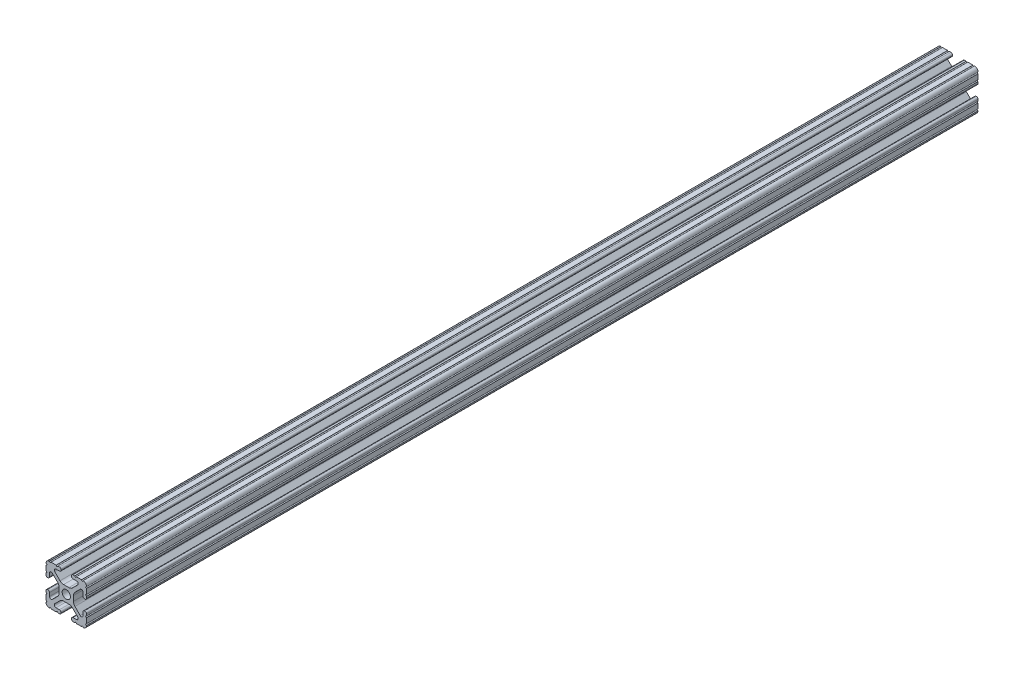
SolidWorks part; units mm, degrees
ref_plane "Front Plane" through (0, 0, 0) normal (0, 0, 1) x (1, 0, 0)
ref_plane "Top Plane" through (0, 0, 0) normal (0, 1, 0) x (1, 0, 0)
ref_plane "Right Plane" through (0, 0, 0) normal (1, 0, 0) x (0, 0, -1)
sketch "Sketch1" plane through (0, 0, 0) normal (0, 0, 1) x (1, 0, 0)
  line L88 (-7.1797, -8.6452) -> (-3.9523, -5.4237)
  line L89 (-1.7093, -4.4958) -> (1.7093, -4.4958)
  line L90 (3.9523, -5.4237) -> (7.1797, -8.6452)
  line L91 (6.4164, -10.4902) -> (4.2875, -10.4902)
  line L92 (3.2385, -11.5392) -> (3.2385, -11.651)
  line L93 (4.2875, -12.7) -> (5.3171, -12.7)
  line L94 (6.3331, -12.7) -> (9.5504, -12.7)
  line L95 (12.7, -9.5504) -> (12.7, -6.3331)
  line L96 (12.7, -5.3171) -> (12.7, -4.2875)
  line L97 (11.651, -3.2385) -> (11.5392, -3.2385)
  line L98 (10.4902, -4.2875) -> (10.4902, -6.4021)
  line L99 (8.7371, -7.1294) -> (5.441, -3.8408)
  line L100 (4.5085, -1.5932) -> (4.5085, 1.5932)
  line L101 (5.441, 3.8408) -> (8.7371, 7.1294)
  line L102 (10.4902, 6.4021) -> (10.4902, 4.2875)
  line L103 (11.5392, 3.2385) -> (11.651, 3.2385)
  line L104 (12.7, 4.2875) -> (12.7, 5.3171)
  line L105 (12.7, 6.3331) -> (12.7, 9.5504)
  line L106 (9.5504, 12.7) -> (6.3331, 12.7)
  line L107 (5.3171, 12.7) -> (4.2875, 12.7)
  line L108 (3.2385, 11.651) -> (3.2385, 11.5392)
  line L109 (4.2875, 10.4902) -> (6.4768, 10.4902)
  line L110 (7.207, 8.7244) -> (3.8983, 5.4232)
  line L111 (1.6558, 4.4958) -> (-1.6558, 4.4958)
  line L112 (-3.8983, 5.4232) -> (-7.207, 8.7244)
  line L113 (-6.4768, 10.4902) -> (-4.2875, 10.4902)
  line L114 (-3.2385, 11.5392) -> (-3.2385, 11.651)
  line L115 (-4.2875, 12.7) -> (-5.3171, 12.7)
  line L116 (-6.3331, 12.7) -> (-9.5504, 12.7)
  line L117 (-12.7, 9.5504) -> (-12.7, 6.3331)
  line L118 (-12.7, 5.3171) -> (-12.7, 4.2875)
  line L119 (-11.651, 3.2385) -> (-11.5392, 3.2385)
  line L120 (-10.4902, 4.2875) -> (-10.4902, 6.4021)
  line L121 (-8.7371, 7.1294) -> (-5.441, 3.8408)
  line L122 (-4.5085, 1.5932) -> (-4.5085, -1.5932)
  line L123 (-5.441, -3.8408) -> (-8.7371, -7.1294)
  line L124 (-10.4902, -6.4021) -> (-10.4902, -4.2875)
  line L125 (-11.5392, -3.2385) -> (-11.651, -3.2385)
  line L126 (-12.7, -4.2875) -> (-12.7, -5.3171)
  line L127 (-12.7, -6.3331) -> (-12.7, -9.5504)
  line L128 (-9.5504, -12.7) -> (-6.3331, -12.7)
  line L129 (-5.3171, -12.7) -> (-4.2875, -12.7)
  line L130 (-3.2385, -11.651) -> (-3.2385, -11.5392)
  line L131 (-4.2875, -10.4902) -> (-6.4164, -10.4902)
  circle A1 centre (0, 0) radius 2.6035
  arc A104 (-7.1797, -8.6452) -> (-6.4164, -10.4902) centre (-6.4164, -9.4098) ccw
  arc A105 (-1.7093, -4.4958) -> (-3.9523, -5.4237) centre (-1.7093, -7.6708) ccw
  arc A106 (3.9523, -5.4237) -> (1.7093, -4.4958) centre (1.7093, -7.6708) ccw
  arc A107 (6.4164, -10.4902) -> (7.1797, -8.6452) centre (6.4164, -9.4098) ccw
  arc A108 (4.2875, -10.4902) -> (3.2385, -11.5392) centre (4.2875, -11.5392) ccw
  arc A109 (3.2385, -11.651) -> (4.2875, -12.7) centre (4.2875, -11.651) ccw
  arc A110 (6.3331, -12.7) -> (5.3171, -12.7) centre (5.8251, -12.7) ccw
  arc A111 (10.5664, -12.6998) -> (9.5504, -12.7) centre (10.0584, -12.7) ccw
  arc A112 (10.5664, -12.6998) -> (12.6998, -10.5664) centre (10.5918, -10.5918) ccw
  arc A113 (12.7, -9.5504) -> (12.6998, -10.5664) centre (12.7, -10.0584) ccw
  arc A114 (12.7, -5.3171) -> (12.7, -6.3331) centre (12.7, -5.8251) ccw
  arc A115 (12.7, -4.2875) -> (11.651, -3.2385) centre (11.651, -4.2875) ccw
  arc A116 (11.5392, -3.2385) -> (10.4902, -4.2875) centre (11.5392, -4.2875) ccw
  arc A117 (8.7371, -7.1294) -> (10.4902, -6.4021) centre (9.4628, -6.4021) ccw
  arc A118 (4.5085, -1.5932) -> (5.441, -3.8408) centre (7.6835, -1.5932) ccw
  arc A119 (5.441, 3.8408) -> (4.5085, 1.5932) centre (7.6835, 1.5932) ccw
  arc A120 (10.4902, 6.4021) -> (8.7371, 7.1294) centre (9.4628, 6.4021) ccw
  arc A121 (10.4902, 4.2875) -> (11.5392, 3.2385) centre (11.5392, 4.2875) ccw
  arc A122 (11.651, 3.2385) -> (12.7, 4.2875) centre (11.651, 4.2875) ccw
  arc A123 (12.7, 6.3331) -> (12.7, 5.3171) centre (12.7, 5.8251) ccw
  arc A124 (12.6998, 10.5664) -> (12.7, 9.5504) centre (12.7, 10.0584) ccw
  arc A125 (12.6998, 10.5664) -> (10.5664, 12.6998) centre (10.5918, 10.5918) ccw
  arc A126 (9.5504, 12.7) -> (10.5664, 12.6998) centre (10.0584, 12.7) ccw
  arc A127 (5.3171, 12.7) -> (6.3331, 12.7) centre (5.8251, 12.7) ccw
  arc A128 (4.2875, 12.7) -> (3.2385, 11.651) centre (4.2875, 11.651) ccw
  arc A129 (3.2385, 11.5392) -> (4.2875, 10.4902) centre (4.2875, 11.5392) ccw
  arc A130 (7.207, 8.7244) -> (6.4768, 10.4902) centre (6.4768, 9.4563) ccw
  arc A131 (1.6558, 4.4958) -> (3.8983, 5.4232) centre (1.6558, 7.6708) ccw
  arc A132 (-3.8983, 5.4232) -> (-1.6558, 4.4958) centre (-1.6558, 7.6708) ccw
  arc A133 (-6.4768, 10.4902) -> (-7.207, 8.7244) centre (-6.4768, 9.4563) ccw
  arc A134 (-4.2875, 10.4902) -> (-3.2385, 11.5392) centre (-4.2875, 11.5392) ccw
  arc A135 (-3.2385, 11.651) -> (-4.2875, 12.7) centre (-4.2875, 11.651) ccw
  arc A136 (-6.3331, 12.7) -> (-5.3171, 12.7) centre (-5.8251, 12.7) ccw
  arc A137 (-10.5664, 12.6998) -> (-9.5504, 12.7) centre (-10.0584, 12.7) ccw
  arc A138 (-10.5664, 12.6998) -> (-12.6998, 10.5664) centre (-10.5918, 10.5918) ccw
  arc A139 (-12.7, 9.5504) -> (-12.6998, 10.5664) centre (-12.7, 10.0584) ccw
  arc A140 (-12.7, 5.3171) -> (-12.7, 6.3331) centre (-12.7, 5.8251) ccw
  arc A141 (-12.7, 4.2875) -> (-11.651, 3.2385) centre (-11.651, 4.2875) ccw
  arc A142 (-11.5392, 3.2385) -> (-10.4902, 4.2875) centre (-11.5392, 4.2875) ccw
  arc A143 (-8.7371, 7.1294) -> (-10.4902, 6.4021) centre (-9.4628, 6.4021) ccw
  arc A144 (-4.5085, 1.5932) -> (-5.441, 3.8408) centre (-7.6835, 1.5932) ccw
  arc A145 (-5.441, -3.8408) -> (-4.5085, -1.5932) centre (-7.6835, -1.5932) ccw
  arc A146 (-10.4902, -6.4021) -> (-8.7371, -7.1294) centre (-9.4628, -6.4021) ccw
  arc A147 (-10.4902, -4.2875) -> (-11.5392, -3.2385) centre (-11.5392, -4.2875) ccw
  arc A148 (-11.651, -3.2385) -> (-12.7, -4.2875) centre (-11.651, -4.2875) ccw
  arc A149 (-12.7, -6.3331) -> (-12.7, -5.3171) centre (-12.7, -5.8251) ccw
  arc A150 (-12.6998, -10.5664) -> (-12.7, -9.5504) centre (-12.7, -10.0584) ccw
  arc A151 (-12.6998, -10.5664) -> (-10.5664, -12.6998) centre (-10.5918, -10.5918) ccw
  arc A152 (-9.5504, -12.7) -> (-10.5664, -12.6998) centre (-10.0584, -12.7) ccw
  arc A153 (-5.3171, -12.7) -> (-6.3331, -12.7) centre (-5.8251, -12.7) ccw
  arc A154 (-4.2875, -12.7) -> (-3.2385, -11.651) centre (-4.2875, -11.651) ccw
  arc A155 (-3.2385, -11.5392) -> (-4.2875, -10.4902) centre (-4.2875, -11.5392) ccw
extrude "Boss-Extrude1" add sketch "Sketch1" along normal mid plane 558.8
